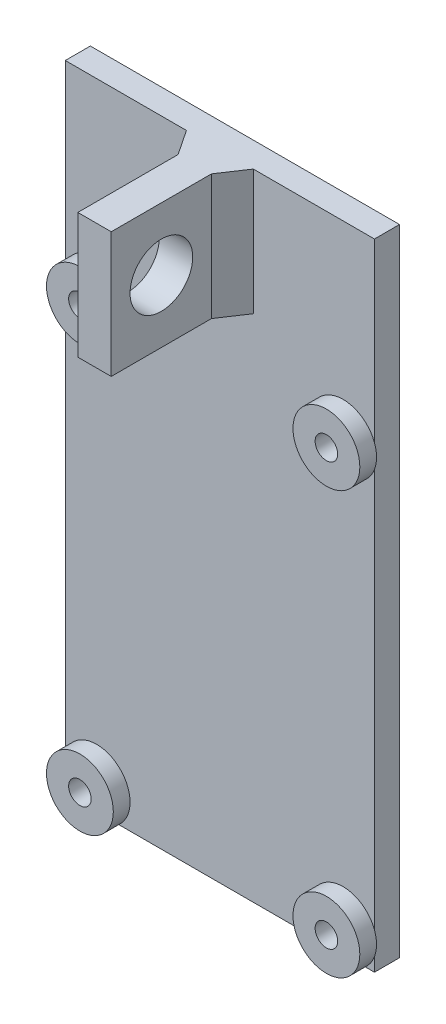
SolidWorks part; units mm, degrees
ref_plane "Plan de face" through (0, 0, 0) normal (0, 0, 1) x (1, 0, 0)
ref_plane "Plan de dessus" through (0, 0, 0) normal (0, 1, 0) x (1, 0, 0)
ref_plane "Plan de droite" through (0, 0, 0) normal (1, 0, 0) x (0, 0, -1)
sketch "Main-Sketch" plane through (0, 0, 0) normal (0, 0, 1) x (1, 0, 0)
  line L1 (0, 0) -> (37, 0)
  line L2 (0, 0) -> (0, 76)
  line L3 (0, 76) -> (37, 76)
  line L4 (37, 0) -> (37, 76)
  dimension "D1" = 37
  dimension "D2" = 76
extrude "Main-Extrusion" add sketch "Main-Sketch" along normal blind 3
sketch "Board-Fix-Sketch" plane through (0, 0, 3) normal (0, 0, 1) x (1, 0, 0)
  line L0 (0, 76) -> (0, 0) construction
  line L1 (37, 0) -> (37, 76) construction
  line L2 (0, 0) -> (37, 0) construction
  circle A0 centre (3.75, 3) radius 4
  circle A1 centre (33.25, 3) radius 4
  circle A2 centre (33.25, 53.5) radius 4
  circle A3 centre (3.75, 53.5) radius 4
  circle A4 centre (3.75, 3) radius 1.35
  circle A5 centre (33.25, 3) radius 1.35
  circle A6 centre (33.25, 53.5) radius 1.35
  circle A7 centre (3.75, 53.5) radius 1.35
  dimension "D4" = 8
  dimension "D5" = 3
  dimension "D7" = 2.7
  dimension "D1" = 3.75
  dimension "D2" = 3.75
  dimension "D3" = 50.5
  dimension "D6" = 29.5
extrude "Board-Fix" add sketch "Board-Fix-Sketch" along normal blind 2
sketch "Jack-Fix-Sketch" plane through (0, 0, 3) normal (0, 0, 1) x (1, 0, 0)
  line L0 (37, 76) -> (0, 76) construction
  line L1 (16.5, 76) -> (20.5, 76)
  line L2 (16.5, 76) -> (16.5, 61)
  line L3 (16.5, 61) -> (20.5, 61)
  line L4 (20.5, 76) -> (20.5, 61)
  point P8 (18.5, 76)
  point P9 (18.5, 76)
  dimension "D1" = 4
  dimension "D2" = 15
extrude "Jack-Fix" add sketch "Jack-Fix-Sketch" along normal blind 15
sketch "Jack-Fix-Hole-Sketch" plane through (20.5, 0, 0) normal (1, 0, 0) x (0, 0, -1)
  line L0 (-18, 61) -> (-18, 76) construction
  circle A0 centre (-12, 68.5) radius 3.75
  point P2 (0, 0)
  point P5 (-18, 68.5)
  dimension "D1" = 7.5
  dimension "D2" = 6
extrude "Jack-Fix-Hole" cut sketch "Jack-Fix-Hole-Sketch" against normal through all
sketch "Jack-Fix-Reinforcement-Sketch" plane through (0, 61, 0) normal (0, -1, 0) x (-1, 0, 0)
  line L0 (-22.5, -3) -> (-14.5, -3)
  line L1 (-14.5, -3) -> (-16.5, -6)
  line L2 (-16.5, -6) -> (-20.5, -6)
  line L3 (-20.5, -6) -> (-22.5, -3)
  line L5 (-16.5, -3) -> (-20.5, -3) construction
  line L6 (-16.5, -18) -> (-16.5, -3) construction
  line L7 (-20.5, -18) -> (-20.5, -3) construction
  point P2 (-14.8552, -1.7787)
  point P7 (-22.2622, -2)
  point P8 (-16.5, -5)
  point P11 (-20.5, -5)
  dimension "D1" = 3
  dimension "D2" = 8
extrude "Jack-Fix-Reinforcement-Extrusion" add sketch "Jack-Fix-Reinforcement-Sketch" against normal up to surface (15 mm away) up to face at (18.5, 76, 6)
